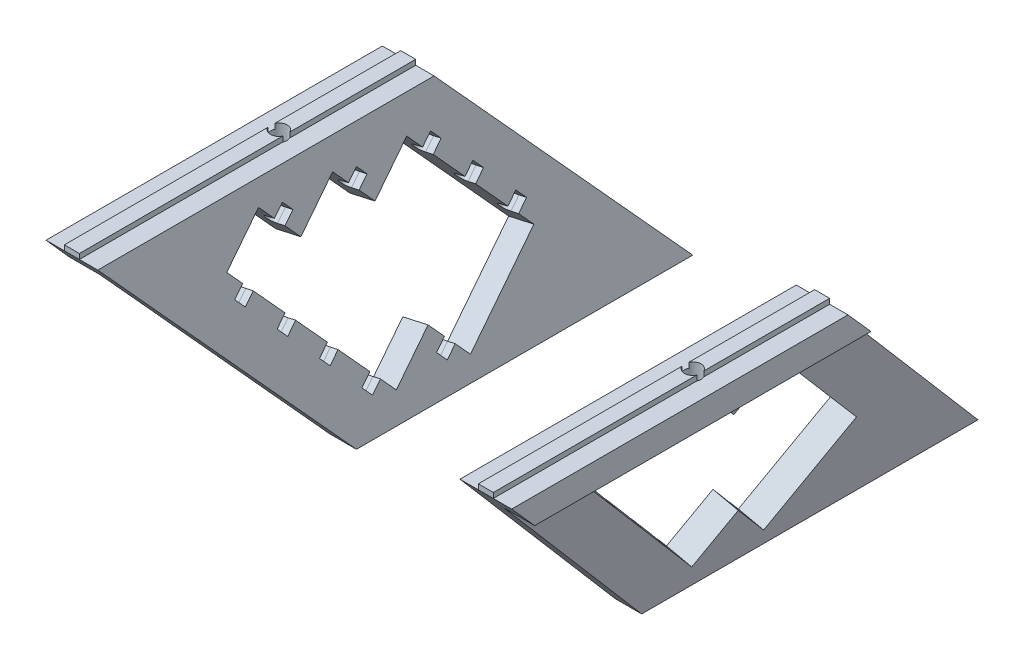
SolidWorks part; units mm, degrees
ref_plane "Front Plane" through (0, 0, 0) normal (0, 0, 1) x (1, 0, 0)
ref_plane "Top Plane" through (0, 0, 0) normal (0, 1, 0) x (1, 0, 0)
ref_plane "Right Plane" through (0, 0, 0) normal (1, 0, 0) x (0, 0, -1)
sketch "Sketch1" plane through (0, 0, 0) normal (0, 0, 1) x (1, 0, 0)
  line L0 (20, 45) -> (20, 40)
  line L1 (20, 40) -> (14.0109, 40)
  line L2 (14.0109, 40) -> (5.122, 0)
  line L3 (5.122, 0) -> (0, 0)
  line L4 (0, 0) -> (10, 45)
  line L5 (10, 45) -> (13.55, 45)
  line L6 (13.55, 45) -> (13.55, 46)
  line L7 (13.55, 46) -> (16.45, 46)
  line L8 (16.45, 46) -> (16.45, 45)
  line L9 (16.45, 45) -> (20, 45)
  line L10 (5.122, 0) -> (34.2968, 0) construction
  dimension "D1" = 10
  dimension "D2" = 2.9
  dimension "D3" = 5
  dimension "D4" = 10
  dimension "D5" = 5
  dimension "D6" = 45
  dimension "D7" = 1
extrude "Main" add sketch "Sketch1" along normal mid plane 105
sketch "Sketch3" plane through (0, 46, 0) normal (0, 1, 0) x (1, 0, 0)
  line L0 (16.45, -52.5) -> (13.55, -52.5) construction
  line L1 (14.0109, -52.5) -> (20, -52.5) construction
  line L2 (20, -52.5) -> (20, 52.5) construction
  circle A0 centre (15, -12.5) radius 1.6
  dimension "D1" = 40
  dimension "D2" = 3.2
  dimension "D4" = 5
extrude "MakerBeamFixHoles" cut sketch "Sketch3" against normal through all
sketch "Sketch2" plane through (0, 40.6155, 0) normal (1, 0, 0) x (0, 0, 1)
  line L0 (-52.5, 40.6155) -> (-12.5, -4.3845)
  line L1 (52.5, -4.3845) -> (-52.5, -4.3845) construction
  line L3 (52.5, 40.6155) -> (-52.5, 40.6155) construction
  line L4 (-12.5, -4.3845) -> (-12.5, -5.3845)
  line L5 (-52.5, 40.6155) -> (-52.5, -5.3845)
  line L6 (52.5, -4.3845) -> (52.5, 40.6155)
  line L7 (52.5, 40.6155) -> (12.5, 40.6155)
  line L8 (12.5, 40.6155) -> (52.5, -4.3845)
  line L9 (52.5, -5.3845) -> (13.1764, -5.3845) construction
  line L10 (-12.5, -5.3845) -> (-52.5, -5.3845)
  dimension "D1" = 40
extrude "SideCut" cut sketch "Sketch2" against normal through all and the other way through all
sketch "Sketch5" plane through (0, 0, 0) normal (-0.9762, 0.2169, 0) x (0, 0, 1)
  line L0 (22.3499, 41.8678) -> (15.796, 34.3149)
  line L1 (22.3499, 41.8678) -> (29.9028, 35.314)
  line L2 (29.9028, 35.314) -> (3.6874, 5.1022)
  line L3 (3.6874, 5.1022) -> (-3.8655, 11.656)
  line L4 (15.796, 34.3149) -> (8.2431, 40.8687)
  line L5 (12.5, 0) -> (52.5, 46.0977) construction
  line L6 (52.5, 46.8678) -> (13.1764, 46.8678) construction
  line L7 (8.2431, 40.8687) -> (1.6892, 33.3158)
  line L8 (1.6892, 33.3158) -> (-5.8637, 39.8696)
  line L9 (-5.8637, 39.8696) -> (-25.5253, 17.2108)
  line L10 (-12.5, 46.0977) -> (-52.5, 0) construction
  line L12 (-3.8655, 11.656) -> (-10.4194, 4.1031)
  line L13 (-10.4194, 4.1031) -> (-25.5253, 17.2108)
  dimension "D1" = 10
  dimension "D2" = 5
  dimension "D3" = 10
  dimension "D4" = 40
  dimension "D5" = 10
  dimension "D6" = 10
  dimension "D7" = 10
  dimension "D8" = 10
  dimension "D9" = 49.0941
extrude "CentralCut" cut sketch "Sketch5" against normal blind 10
ref_plane "Plane1" through (0.7903, 3.5564, -4.1985) normal (0.1422, 0.6398, -0.7553) x (-0.9898, 0.0919, -0.1085)
sketch "Sketch4" plane through (0.0794, 7.8576, 5.931) normal (-0.1422, -0.6398, 0.7553) x (-0.9898, 0.0919, -0.1085)
  line L0 (-1.0379, 3.6453) -> (-7.659, -35.8029) construction
  line L1 (-12.5901, -34.9752) -> (-7.659, -35.8029) construction
  line L2 (-6.6245, -29.6391) -> (-7.0383, -32.1046)
  line L3 (-7.0383, -32.1046) -> (-8.5176, -31.8563)
  line L5 (-6.6245, -29.6391) -> (-8.1038, -29.3908)
  arc A1 (-8.1038, -29.3908) -> (-8.5176, -31.8563) centre (-8.3107, -30.6235) ccw
  dimension "D1" = 1.5
  dimension "D2" = 1.25
  dimension "D3" = 5
extrude "RollerSupportHoles" cut sketch "Sketch4" along normal blind 2.5
ref_plane "MirrorPlane" through (-25, 0, 0) normal (1, 0, 0) x (0, 0, -1)
pattern_linear "LPattern1" count 4 spacing 10 along (-0.1638, -0.7373, -0.6554) of "RollerSupportHoles"
sketch "Sketch6" plane through (-0.276, -1.2419, 1.4662) normal (0.1422, 0.6398, -0.7553) x (-0.9898, 0.0919, -0.1085)
  line L0 (-5.383, 32.0717) -> (-4.9692, 29.6062)
  line L1 (-4.9692, 29.6062) -> (-6.4485, 29.3579)
  line L2 (-5.383, 32.0717) -> (-6.8623, 31.8234)
  arc A0 (-6.8623, 31.8234) -> (-6.4485, 29.3579) centre (-6.6554, 30.5907) ccw
  arc A1 (-6.8623, 31.8234) -> (-6.4485, 29.3579) centre (-6.6554, 30.5907) ccw construction
extrude "Cut-Extrude1" cut sketch "Sketch6" along normal blind 25
mirror "Mirror5" about plane through (0.7903, 3.5564, -4.1985) normal (0.1422, 0.6398, -0.7553) of "RollerSupportHoles"
sketch "Sketch7" plane through (-0.276, -1.2419, 1.4662) normal (0.1422, 0.6398, -0.7553) x (-0.9898, 0.0919, -0.1085)
  line L0 (-4.7932, 19.4959) -> (-3.3139, 19.7442)
  line L1 (-3.3139, 19.7442) -> (-3.7277, 22.2097)
  line L2 (-3.7277, 22.2097) -> (-5.207, 21.9614)
  arc A0 (-5.207, 21.9614) -> (-4.7932, 19.4959) centre (-5.0001, 20.7286) ccw
  arc A1 (-5.207, 21.9614) -> (-4.7932, 19.4959) centre (-5.0001, 20.7286) ccw construction
extrude "Cut-Extrude2" cut sketch "Sketch7" along normal blind 35
sketch "Sketch8" plane through (-0.276, -1.2419, 1.4662) normal (0.1422, 0.6398, -0.7553) x (-0.9898, 0.0919, -0.1085)
  line L0 (-3.138, 9.6338) -> (-1.6586, 9.8821)
  line L1 (-1.6586, 9.8821) -> (-2.0725, 12.3476)
  line L2 (-2.0725, 12.3476) -> (-3.5518, 12.0993)
  arc A0 (-3.5518, 12.0993) -> (-3.138, 9.6338) centre (-3.3449, 10.8666) ccw
extrude "Cut-Extrude3" cut sketch "Sketch8" along normal blind 35
sketch "Sketch9" plane through (4.3446, 19.5509, -23.0809) normal (-0.1422, -0.6398, 0.7553) x (0.9898, -0.0919, 0.1085)
  line L0 (-0.0221, -0.1317) -> (1.4779, -0.3834)
  line L1 (1.6586, 9.8821) -> (-0.6174, -3.6782) construction
  line L2 (-0.0221, -0.1317) -> (0.3975, 2.3683)
  line L3 (0.3975, 2.3683) -> (1.8975, 2.1166)
  arc A0 (1.4779, -0.3834) -> (1.8975, 2.1166) centre (1.6877, 0.8666) ccw
  arc A1 (3.138, 9.6338) -> (3.5518, 12.0993) centre (3.3449, 10.8666) ccw construction
  dimension "D3" = 10
  dimension "D1" = 2.5
  dimension "D2" = 1.5
extrude "Cut-Extrude4" cut sketch "Sketch9" against normal blind 2.5
sketch "Sketch10" plane through (0, 40, 0) normal (0, -1, 0) x (1, 0, 0)
  circle A2 centre (15, 12.5) radius 4.25
  arc A3 (14.0109, 11.2424) -> (14.0109, 13.7576) centre (15, 12.5) ccw construction
extrude "Cut-Extrude5" cut sketch "Sketch10" along normal blind 5
mirror "Mirror6" about plane through (18.6275, 37.7262, 8.2431) normal (0.1422, 0.6398, -0.7553) of "Cut-Extrude4"
mirror "Mirror4" about plane through (-25, 0, 0) normal (1, 0, 0) of bodies 121 112
